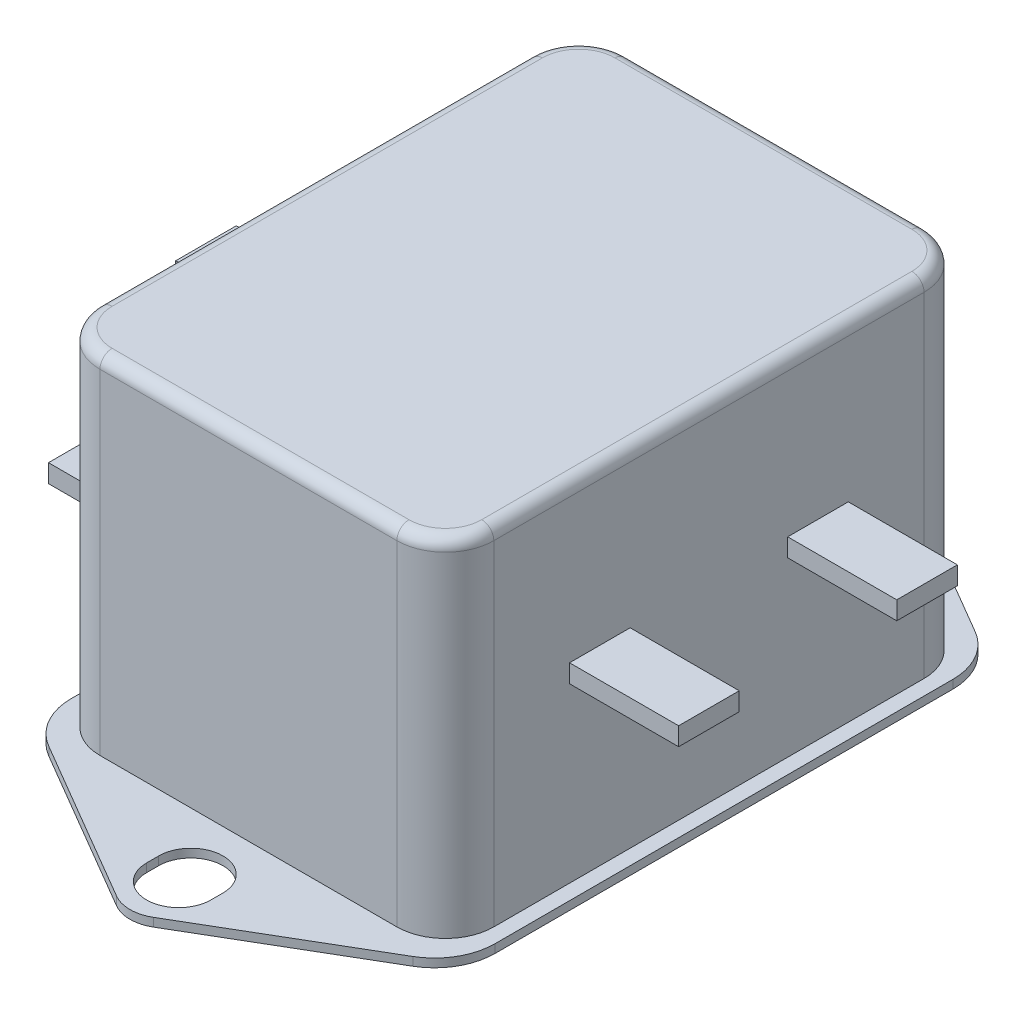
SolidWorks part; units mm, degrees
ref_plane "Front Plane" through (0, 0, 0) normal (0, 0, 1) x (1, 0, 0)
ref_plane "Top Plane" through (0, 0, 0) normal (0, 1, 0) x (1, 0, 0)
ref_plane "Right Plane" through (0, 0, 0) normal (1, 0, 0) x (0, 0, -1)
sketch "Sketch1" plane through (0, 0, 0) normal (0, 1, 0) x (1, 0, 0)
  line L0 (0, 0) -> (0, 27) construction
  line L1 (0, 0) -> (0, -27) construction
  line L2 (0, 27.5) -> (0, 26.5) construction
  line L3 (2.65, 27.5) -> (2.65, 26.5)
  line L4 (-17.5, 0) -> (-17.5, 18.884)
  line L5 (17.5, 0) -> (17.5, 18.884)
  line L6 (-17.5, 0) -> (-17.5, -18.884)
  line L7 (17.5, 0) -> (17.5, -18.884)
  line L8 (-15.027, 23.1985) -> (-1.5162, 31.1119)
  line L9 (1.5162, 31.1119) -> (15.027, 23.1985)
  line L10 (-15.027, -23.1985) -> (-1.5162, -31.1119)
  line L11 (1.5162, -31.1119) -> (15.027, -23.1985)
  line L12 (-2.65, 27.5) -> (-2.65, 26.5)
  line L13 (0, -26.5) -> (0, -27.5) construction
  line L14 (2.65, -26.5) -> (2.65, -27.5)
  line L15 (-2.65, -26.5) -> (-2.65, -27.5)
  arc A0 (2.65, 27.5) -> (-2.65, 27.5) centre (0, 27.5) ccw
  arc A1 (-2.65, 26.5) -> (2.65, 26.5) centre (0, 26.5) ccw
  arc A2 (2.65, -26.5) -> (-2.65, -26.5) centre (0, -26.5) ccw
  arc A3 (-2.65, -27.5) -> (2.65, -27.5) centre (0, -27.5) ccw
  arc A4 (1.5162, -31.1119) -> (-1.5162, -31.1119) centre (0, -28.5233) cw
  arc A5 (1.5162, 31.1119) -> (-1.5162, 31.1119) centre (0, 28.5233) ccw
  arc A6 (-17.5, -18.884) -> (-15.027, -23.1985) centre (-12.5, -18.884) ccw
  arc A7 (17.5, -18.884) -> (15.027, -23.1985) centre (12.5, -18.884) cw
  arc A8 (17.5, 18.884) -> (15.027, 23.1985) centre (12.5, 18.884) ccw
  arc A9 (-17.5, 18.884) -> (-15.027, 23.1985) centre (-12.5, 18.884) cw
  point P16 (0, 27)
  point P23 (0, -27)
  point P28 (0, -32)
  point P31 (0, 32)
  point P34 (-17.5, -21.75)
  point P41 (-17.5, 21.75)
  dimension "D4" = 3
  dimension "D7" = 5
  dimension "D1" = 27
  dimension "D2" = 27
  dimension "D3" = 5.3
  dimension "D5" = 21.75
  dimension "D6" = 21.75
extrude "Boss-Extrude1" add sketch "Sketch1" along normal blind 0.7
sketch "Sketch2" plane through (0, 0.7, 0) normal (0, 1, 0) x (1, 0, 0)
  line L0 (0, 0) -> (-16.25, 0) construction
  line L1 (0, 0) -> (16.25, 0) construction
  line L2 (0, 0) -> (0, 21.75) construction
  line L3 (0, 0) -> (0, -21.75) construction
  line L5 (-12.25, 21.75) -> (12.25, 21.75)
  line L6 (-16.25, 17.75) -> (-16.25, -17.75)
  line L7 (-12.25, -21.75) -> (12.25, -21.75)
  line L8 (16.25, 17.75) -> (16.25, -17.75)
  arc A0 (-16.25, -17.75) -> (-12.25, -21.75) centre (-12.25, -17.75) ccw
  arc A1 (12.25, -21.75) -> (16.25, -17.75) centre (12.25, -17.75) ccw
  arc A2 (12.25, 21.75) -> (16.25, 17.75) centre (12.25, 17.75) cw
  arc A3 (-12.25, 21.75) -> (-16.25, 17.75) centre (-12.25, 17.75) ccw
  dimension "D5" = 4
  dimension "D1" = 16.25
  dimension "D2" = 16.25
  dimension "D3" = 21.75
  dimension "D4" = 21.75
extrude "Boss-Extrude2" add sketch "Sketch2" along normal blind 28.6
sketch "Sketch3" plane through (-16.25, 0, 0) normal (-1, 0, 0) x (0, 0, 1)
  line L0 (0, 0.7) -> (0, 10) construction
  line L1 (-18.884, 0.7) -> (18.884, 0.7) construction
  line L2 (0, 10) -> (-10.5, 10) construction
  line L3 (0, 10) -> (10.5, 10) construction
  line L5 (-13, 10.75) -> (-8, 10.75)
  line L6 (-13, 10.75) -> (-13, 9.25)
  line L7 (-13, 9.25) -> (-8, 9.25)
  line L8 (-8, 10.75) -> (-8, 9.25)
  line L9 (-10.5, 9.25) -> (-10.5, 10.75) construction
  line L10 (-13, 10) -> (-8, 10) construction
  line L11 (8, 10.75) -> (13, 10.75)
  line L12 (8, 10.75) -> (8, 9.25)
  line L13 (8, 9.25) -> (13, 9.25)
  line L14 (13, 10.75) -> (13, 9.25)
  line L15 (10.5, 9.25) -> (10.5, 10.75) construction
  line L16 (8, 10) -> (13, 10) construction
  line L17 (-2.5, 19.9301) -> (2.5, 19.9301)
  line L18 (-2.5, 19.9301) -> (-2.5, 18.4301)
  line L19 (-2.5, 18.4301) -> (2.5, 18.4301)
  line L20 (2.5, 19.9301) -> (2.5, 18.4301)
  line L21 (0, 18.4301) -> (0, 19.9301) construction
  line L22 (-2.5, 19.1801) -> (2.5, 19.1801) construction
  point P13 (0, 19.1801)
  dimension "D1" = 9.3
  dimension "D2" = 10.5
  dimension "D3" = 10.5
  dimension "D4" = 5
  dimension "D5" = 1.5
  dimension "D6" = 1.5
  dimension "D7" = 5
  dimension "D8" = 5
  dimension "D9" = 1.5
extrude "Boss-Extrude3" add sketch "Sketch3" along normal blind 9
sketch "Sketch4" plane through (16.25, 0, 0) normal (1, 0, 0) x (0, 0, -1)
  line L0 (0, 0.7) -> (0, 15.7) construction
  line L1 (-18.884, 0.7) -> (18.884, 0.7) construction
  line L2 (0, 15.7) -> (-9, 15.7) construction
  line L3 (0, 15.7) -> (9, 15.7) construction
  line L5 (-11.5, 16.45) -> (-6.5, 16.45)
  line L6 (-11.5, 16.45) -> (-11.5, 14.95)
  line L7 (-11.5, 14.95) -> (-6.5, 14.95)
  line L8 (-6.5, 16.45) -> (-6.5, 14.95)
  line L9 (-9, 14.95) -> (-9, 16.45) construction
  line L10 (-11.5, 15.7) -> (-6.5, 15.7) construction
  line L11 (6.5, 16.45) -> (11.5, 16.45)
  line L12 (6.5, 16.45) -> (6.5, 14.95)
  line L13 (6.5, 14.95) -> (11.5, 14.95)
  line L14 (11.5, 16.45) -> (11.5, 14.95)
  line L15 (9, 14.95) -> (9, 16.45) construction
  line L16 (6.5, 15.7) -> (11.5, 15.7) construction
  dimension "D1" = 15
  dimension "D2" = 9
  dimension "D3" = 9
  dimension "D4" = 1.5
  dimension "D5" = 1.5
  dimension "D6" = 5
  dimension "D7" = 5
extrude "Boss-Extrude4" add sketch "Sketch4" along normal blind 9
fillet "Fillet1" radius 1 8 edges at (15.0784, 29.3, -20.5784) (16.25, 29.3, 0) (15.0784, 29.3, 20.5784) (0, 29.3, 21.75) (-15.0784, 29.3, 20.5784) (-16.25, 29.3, 0) (-15.0784, 29.3, -20.5784) (0, 29.3, -21.75)
sketch "Sketch5" plane through (0, 0, 0) normal (0, -1, 0) x (1, 0, 0)
  line L0 (0, 0) -> (0, -22.5024) construction
  line L1 (0, 0) -> (0, 21.8205) construction
  line L2 (0, 0) -> (-15.2147, 0) construction
  line L3 (0, 0) -> (13.5952, 0) construction
sketch "Sketch6" plane through (0, 0, 0) normal (0, -1, 0) x (1, 0, 0)
  point P28 (0, -27)
  point P29 (0, 27)
